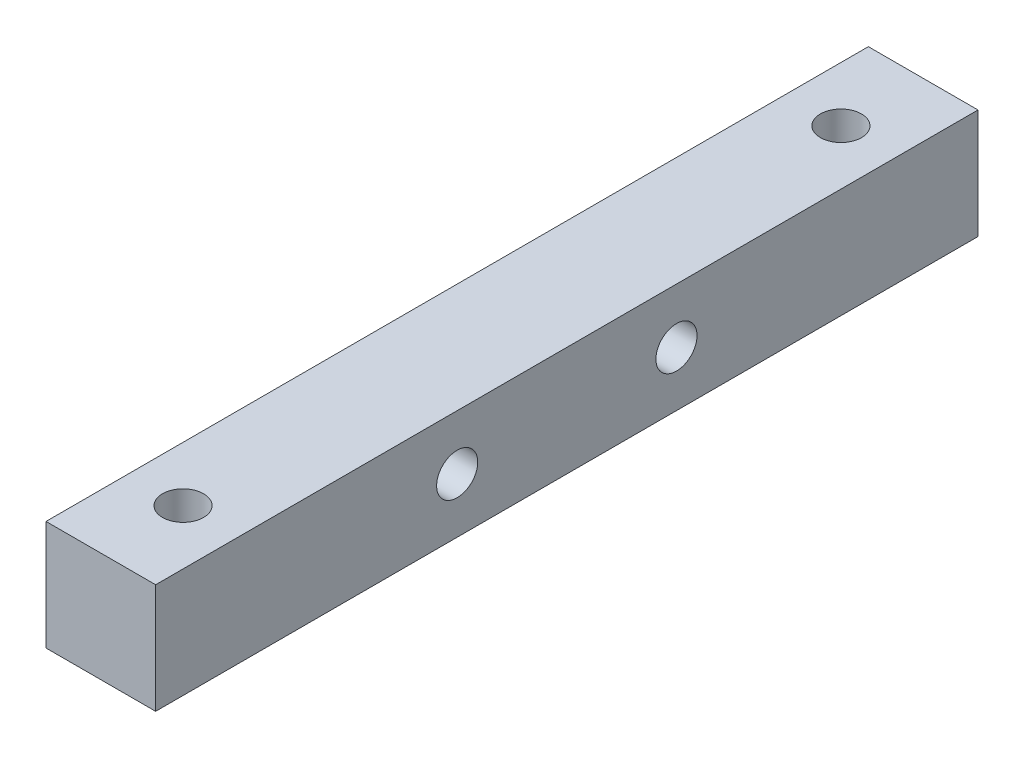
SolidWorks part; units mm, degrees
ref_plane "Alzado" through (0, 0, 0) normal (0, 0, 1) x (1, 0, 0)
ref_plane "Planta" through (0, 0, 0) normal (0, 1, 0) x (1, 0, 0)
ref_plane "Vista lateral" through (0, 0, 0) normal (1, 0, 0) x (0, 0, -1)
sketch "Croquis1" plane through (0, 0, 0) normal (0, 0, 1) x (1, 0, 0)
  line L1 (-5, 5) -> (5, 5)
  line L2 (-5, 5) -> (-5, -5)
  line L3 (-5, -5) -> (5, -5)
  line L4 (5, 5) -> (5, -5)
  line L5 (-5, 5) -> (5, -5) construction
  line L6 (-5, -5) -> (5, 5) construction
  point P0 (0, 0)
  dimension "D1" = 10
  dimension "D2" = 10
extrude "Saliente-Extruir1" add sketch "Croquis1" along normal mid plane 75
sketch "Croquis2" plane through (0, 5, 0) normal (0, 1, 0) x (1, 0, 0)
  line L0 (0, -10) -> (0, 10) construction
  point P0 (0, 0)
  point P4 (0, 0)
  point P5 (0, 10)
  point P7 (0, -10)
  dimension "D1" = 20
sketch "Croquis3" plane through (-5, 0, 0) normal (-1, 0, 0) x (0, 0, 1)
  line L0 (-30, 0) -> (30, 0) construction
  point P4 (0, 0)
  dimension "D1" = 60
hole_wizard "Taladro de margen para M31" [suppressed] positions "Croquis4" profile "Croquis5" hole size "M3" standard "DIN"
sketch "Croquis4" plane through (0, 5, 0) normal (0, 1, 0) x (1, 0, 0)
  point P0 (0, -10)
  point P3 (0, 0)
  point P6 (0, 10)
sketch "Croquis5" plane through (0, 5, 10) normal (1, 0, 0) x (0, 0, 1)
  line L0 (0, 0) -> (0, 10)
  line L1 (0, 10) -> (1.875, 10)
  line L2 (1.875, 10) -> (1.875, 0)
  line L5 (1.875, 0) -> (0, 0)
  line L11 (0, -6.35) -> (0, 107.95) construction
  dimension "Diámetro de taladro hasta el siguiente" = 3.75
  dimension "Profundidad de taladro hasta el siguiente" = 10
sketch "Croquis7" [suppressed] plane through (0, -5, 0) normal (0, -1, 0) x (1, 0, 0)
  line L1 (2.7713, -8.4) -> (0, -6.8)
  line L2 (0, -6.8) -> (-2.7713, -8.4)
  line L3 (-2.7713, -8.4) -> (-2.7713, -11.6)
  line L4 (-2.7713, -11.6) -> (0, -13.2)
  line L5 (0, -13.2) -> (2.7713, -11.6)
  line L6 (2.7713, -11.6) -> (2.7713, -8.4)
  line L7 (2.7713, -1.6) -> (2.7713, 1.6)
  line L8 (2.7713, 1.6) -> (0, 3.2)
  line L9 (0, 3.2) -> (-2.7713, 1.6)
  line L10 (-2.7713, 1.6) -> (-2.7713, -1.6)
  line L11 (-2.7713, -1.6) -> (0, -3.2)
  line L12 (0, -3.2) -> (2.7713, -1.6)
  line L13 (2.7713, 8.4) -> (2.7713, 11.6)
  line L14 (2.7713, 11.6) -> (0, 13.2)
  line L15 (0, 13.2) -> (-2.7713, 11.6)
  line L16 (-2.7713, 11.6) -> (-2.7713, 8.4)
  line L17 (-2.7713, 8.4) -> (0, 6.8)
  line L18 (0, 6.8) -> (2.7713, 8.4)
  circle A0 centre (0, -10) radius 2.7713 construction
  circle A1 centre (0, 0) radius 2.7713 construction
  circle A2 centre (0, 10) radius 2.7713 construction
  dimension "D1" = 3.2
extrude "Cortar-Extruir1" [suppressed] cut sketch "Croquis7" against normal blind 3
hole_wizard "Taladro de margen para M32" [suppressed] positions "Croquis8" profile "Croquis9" hole size "M3" standard "DIN"
sketch "Croquis8" plane through (-5, 0, 0) normal (-1, 0, 0) x (0, 0, 1)
  point P0 (-30, 0)
  point P3 (30, 0)
sketch "Croquis9" plane through (-5, 0, -30) normal (0, 1, 0) x (0, 0, 1)
  line L0 (0, 0) -> (0, 10)
  line L1 (0, 10) -> (1.875, 10)
  line L2 (1.875, 10) -> (1.875, 0)
  line L5 (1.875, 0) -> (0, 0)
  line L11 (0, -6.35) -> (0, 107.95) construction
  dimension "Diámetro de taladro hasta el siguiente" = 3.75
  dimension "Profundidad de taladro hasta el siguiente" = 10
sketch "Croquis10" plane through (-5, 0, 0) normal (-1, 0, 0) x (0, 0, 1)
  line L1 (-28.4, -2.7713) -> (-26.8, 0)
  line L2 (-26.8, 0) -> (-28.4, 2.7713)
  line L3 (-28.4, 2.7713) -> (-31.6, 2.7713)
  line L4 (-31.6, 2.7713) -> (-33.2, 0)
  line L5 (-33.2, 0) -> (-31.6, -2.7713)
  line L6 (-31.6, -2.7713) -> (-28.4, -2.7713)
  line L7 (31.6, -2.7713) -> (33.2, 0)
  line L8 (33.2, 0) -> (31.6, 2.7713)
  line L9 (31.6, 2.7713) -> (28.4, 2.7713)
  line L10 (28.4, 2.7713) -> (26.8, 0)
  line L11 (26.8, 0) -> (28.4, -2.7713)
  line L12 (28.4, -2.7713) -> (31.6, -2.7713)
  circle A0 centre (-30, 0) radius 2.7713 construction
  circle A1 centre (30, 0) radius 2.7713 construction
  dimension "D1" = 3.2
extrude "Cortar-Extruir2" [suppressed] cut sketch "Croquis10" against normal blind 3
sketch "Croquis11" plane through (-5, 0, 0) normal (-1, 0, 0) x (0, 0, 1)
  line L0 (-10, 0) -> (10, 0) construction
  point P4 (0, 0)
  dimension "D1" = 20
hole_wizard "Taladro de margen para M33" positions "Croquis12" profile "Croquis13" hole size "M3" standard "DIN" end condition through all
sketch "Croquis12" plane through (-5, 0, 0) normal (-1, 0, 0) x (0, 0, 1)
  point P0 (-10, 0)
  point P3 (10, 0)
sketch "Croquis13" plane through (-5, 0, -10) normal (0, 1, 0) x (0, 0, 1)
  line L0 (0, 0) -> (0, 10)
  line L1 (0, 10) -> (1.875, 10)
  line L2 (1.875, 10) -> (1.875, 0)
  line L5 (1.875, 0) -> (0, 0)
  line L11 (0, -6.35) -> (0, 107.95) construction
  dimension "Diámetro de taladro hasta el siguiente" = 3.75
  dimension "Profundidad de taladro hasta el siguiente" = 10
ref_plane "Plano1" through (0, 0, 0) normal (-1, 0, 0) x (0, 0, 1)
sketch "Croquis16" plane through (0, -5, 0) normal (0, -1, 0) x (1, 0, 0)
  line L0 (0, -30) -> (0, 30) construction
  point P4 (0, 0)
hole_wizard "Taladro de margen para M34" positions "Croquis17" profile "Croquis18" hole size "M3" standard "DIN" end condition through all
sketch "Croquis17" plane through (0, -5, 0) normal (0, -1, 0) x (-1, 0, 0)
  point P0 (0, 30)
  point P3 (0, -30)
sketch "Croquis18" plane through (0, -5, -30) normal (1, 0, 0) x (0, 0, -1)
  line L0 (0, 0) -> (0, 10)
  line L1 (0, 10) -> (1.875, 10)
  line L2 (1.875, 10) -> (1.875, 0)
  line L5 (1.875, 0) -> (0, 0)
  line L11 (0, -6.35) -> (0, 107.95) construction
  dimension "Diámetro de taladro hasta el siguiente" = 3.75
  dimension "Profundidad de taladro hasta el siguiente" = 10
sketch "Croquis19" plane through (0, -5, 0) normal (0, -1, 0) x (1, 0, 0)
  line L1 (2.7713, -28.4) -> (0, -26.8)
  line L2 (0, -26.8) -> (-2.7713, -28.4)
  line L3 (-2.7713, -28.4) -> (-2.7713, -31.6)
  line L4 (-2.7713, -31.6) -> (0, -33.2)
  line L5 (0, -33.2) -> (2.7713, -31.6)
  line L6 (2.7713, -31.6) -> (2.7713, -28.4)
  line L7 (2.7713, 31.6) -> (0, 33.2)
  line L8 (0, 33.2) -> (-2.7713, 31.6)
  line L9 (-2.7713, 31.6) -> (-2.7713, 28.4)
  line L10 (-2.7713, 28.4) -> (0, 26.8)
  line L11 (0, 26.8) -> (2.7713, 28.4)
  line L12 (2.7713, 28.4) -> (2.7713, 31.6)
  circle A0 centre (0, -30) radius 2.7713 construction
  circle A1 centre (0, 30) radius 2.7713 construction
  dimension "D1" = 3.2
extrude "Cortar-Extruir4" cut sketch "Croquis19" against normal blind 3.2
sketch "Croquis20" plane through (-5, 0, 0) normal (-1, 0, 0) x (0, 0, 1)
  line L1 (-8.4, -2.7713) -> (-6.8, 0)
  line L2 (-6.8, 0) -> (-8.4, 2.7713)
  line L3 (-8.4, 2.7713) -> (-11.6, 2.7713)
  line L4 (-11.6, 2.7713) -> (-13.2, 0)
  line L5 (-13.2, 0) -> (-11.6, -2.7713)
  line L6 (-11.6, -2.7713) -> (-8.4, -2.7713)
  line L7 (11.6, -2.7713) -> (13.2, 0)
  line L8 (13.2, 0) -> (11.6, 2.7713)
  line L9 (11.6, 2.7713) -> (8.4, 2.7713)
  line L10 (8.4, 2.7713) -> (6.8, 0)
  line L11 (6.8, 0) -> (8.4, -2.7713)
  line L12 (8.4, -2.7713) -> (11.6, -2.7713)
  circle A0 centre (-10, 0) radius 2.7713 construction
  circle A1 centre (10, 0) radius 2.7713 construction
  dimension "D1" = 3.2
extrude "Cortar-Extruir5" cut sketch "Croquis20" against normal blind 3.2
